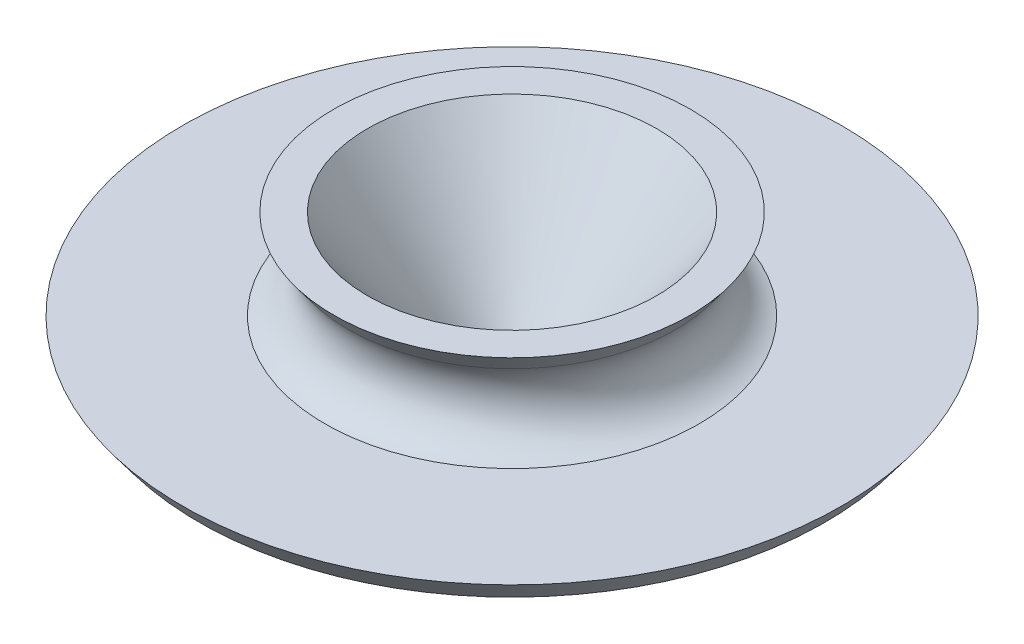
SolidWorks part; units mm, degrees
ref_plane "Front Plane" through (0, 0, 0) normal (0, 0, 1) x (1, 0, 0)
ref_plane "Top Plane" through (0, 0, 0) normal (0, 1, 0) x (1, 0, 0)
ref_plane "Right Plane" through (0, 0, 0) normal (1, 0, 0) x (0, 0, -1)
sketch "Sketch1" plane through (0, 0, 0) normal (0, 0, 1) x (1, 0, 0)
  line L1 (-0.9151, -47.6827) -> (-21.9357, -47.6827)
  line L2 (-21.9357, -47.6827) -> (-26.6462, -41.3327)
  line L3 (-26.6462, -41.3327) -> (-76.7832, -41.3327)
  line L4 (-76.7832, -41.3327) -> (-81.4937, -34.9827)
  line L5 (-81.4937, -34.9827) -> (-41.1864, -34.9827)
  line L6 (-0.9151, -47.6827) -> (-29.178, -9.5827)
  line L7 (-29.178, -9.5827) -> (-38.703, -9.5827)
  line L8 (-38.703, -9.5827) -> (-34.5224, -15.2185)
  line L9 (11.7849, -49.7037) -> (11.7849, 68.1006) construction
  arc A0 (-34.5224, -15.2185) -> (-41.1864, -34.9827) centre (-44.7224, -22.7849) cw
  dimension "D6" = 12.7
  dimension "D1" = 57.15
  dimension "D2" = 9.525
  dimension "D3" = 6.35
  dimension "D4" = 6.35
  dimension "D5" = 38.1
  dimension "D7" = 12.7
revolve "Revolve1" add sketch "Sketch1" angle 360 about L9
